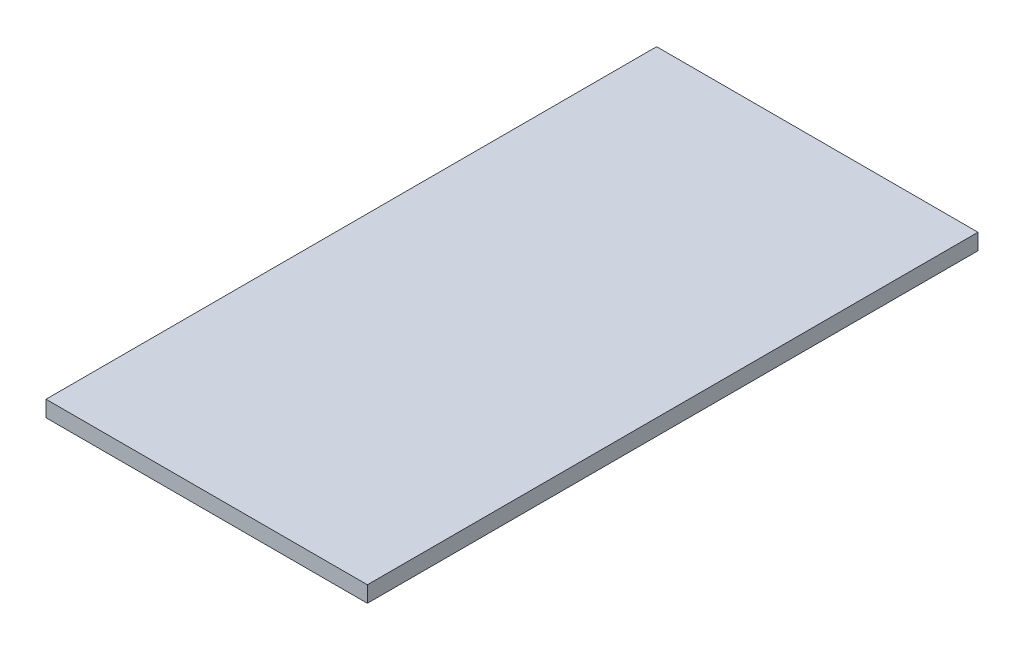
SolidWorks part; units mm, degrees
ref_plane "Front Plane" through (0, 0, 0) normal (0, 0, 1) x (1, 0, 0)
ref_plane "Top Plane" through (0, 0, 0) normal (0, 1, 0) x (1, 0, 0)
ref_plane "Right Plane" through (0, 0, 0) normal (1, 0, 0) x (0, 0, -1)
sketch "Sketch1" plane through (0, 0, 0) normal (0, 1, 0) x (1, 0, 0)
  line L1 (-10, 19) -> (10, 19)
  line L2 (-10, 19) -> (-10, -19)
  line L3 (-10, -19) -> (10, -19)
  line L4 (10, 19) -> (10, -19)
  line L5 (-10, 19) -> (10, -19) construction
  line L6 (-10, -19) -> (10, 19) construction
  point P0 (0, 0)
  dimension "D1" = 20
  dimension "D2" = 38
extrude "Boss-Extrude1" add sketch "Sketch1" along normal blind 1
